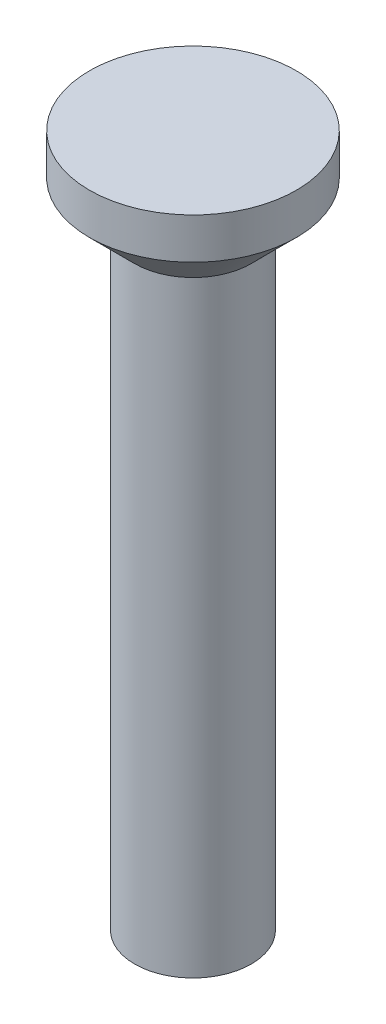
SolidWorks part; units mm, degrees
ref_plane "Спереди" through (0, 0, 0) normal (0, 0, 1) x (1, 0, 0)
ref_plane "Сверху" through (0, 0, 0) normal (0, 1, 0) x (1, 0, 0)
ref_plane "Справа" through (0, 0, 0) normal (1, 0, 0) x (0, 0, -1)
sketch "Эскиз1" plane through (0, 0, 0) normal (0, 0, 1) x (1, 0, 0)
  line L0 (0, 0) -> (25, 0)
  line L1 (25, 0) -> (25, 260)
  line L2 (25, 260) -> (44.354, 279.354)
  line L3 (44.354, 279.354) -> (44.354, 296.9242)
  line L4 (44.354, 296.9242) -> (0, 296.9242)
  line L5 (0, 348.0804) -> (0, -11.7867) construction
  line L6 (0, 0) -> (0, 296.9242)
revolve "Повернуть1" add sketch "Эскиз1" angle 360 about L5
